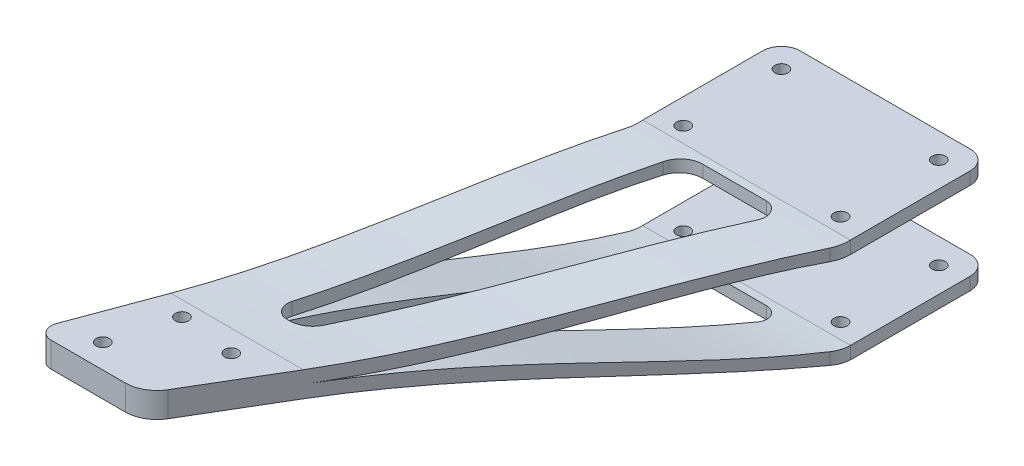
SolidWorks part; units mm, degrees
ref_plane "Front Plane" through (0, 0, 0) normal (0, 0, 1) x (1, 0, 0)
ref_plane "Top Plane" through (0, 0, 0) normal (0, 1, 0) x (1, 0, 0)
ref_plane "Right Plane" through (0, 0, 0) normal (1, 0, 0) x (0, 0, -1)
sketch "Sketch1" plane through (0, 0, 0) normal (0, 1, 0) x (1, 0, 0)
  line L0 (48.255, 28.1) -> (98.255, 28.1) construction
  line L1 (0, 0) -> (148.3533, 0) construction
  line L2 (0, 0) -> (0, 25) construction
  line L3 (0, 25) -> (148.3533, 25) construction
  line L4 (148.3533, 0) -> (148.3533, 25) construction
  line L5 (48.255, -3.1) -> (98.255, -3.1) construction
  line L6 (48.255, 26) -> (98.255, 26) construction
  line L7 (0, 12.5) -> (148.3533, 12.5) construction
  line L8 (-66.4765, -150) -> (240.8263, -150) construction
  line L9 (75.1995, 36.1) -> (100.255, 36.1)
  line L10 (106.255, 30.1) -> (106.255, -7.9752)
  line L11 (104.8547, -13.0786) -> (26.5055, -145.1034)
  line L12 (17.9058, -150) -> (-5.6524, -150)
  line L13 (-9.4032, -144.6102) -> (39.6319, -12.2766)
  line L14 (40.255, -8.8021) -> (40.255, 30.1)
  line L15 (46.255, 36.1) -> (75.1995, 36.1)
  circle A0 centre (48.255, 28.1) radius 2.1
  circle A1 centre (98.255, 28.1) radius 2.1
  circle A2 centre (98.255, -3.1) radius 2.1
  circle A3 centre (48.255, -3.1) radius 2.1
  arc A4 (100.255, 36.1) -> (106.255, 30.1) centre (100.255, 30.1) cw
  arc A5 (40.255, 30.1) -> (46.255, 36.1) centre (46.255, 30.1) cw
  arc A6 (26.5055, -145.1034) -> (17.9058, -150) centre (17.9058, -140) cw
  arc A7 (106.255, -7.9752) -> (104.8547, -13.0786) centre (96.255, -7.9752) cw
  arc A8 (39.6319, -12.2766) -> (40.255, -8.8021) centre (30.255, -8.8021) ccw
  arc A9 (-5.6524, -150) -> (-9.4032, -144.6102) centre (-5.6524, -146) cw
  point P32 (23.5997, -150)
  point P39 (-11.4003, -150)
  dimension "D2" = 4.2
  dimension "D7" = 8
  dimension "D10" = 6
  dimension "D11" = 10
  dimension "D12" = 4
  dimension "D1" = 25
  dimension "D3" = 1
  dimension "D4" = 50
  dimension "D5" = 150
  dimension "D6" = 35
  dimension "D8" = 8
  dimension "D9" = 8
extrude "Boss-Extrude1" add sketch "Sketch1" along normal blind 33
sketch "Sketch2" plane through (0, 33, 0) normal (0, 1, 0) x (1, 0, 0)
  line L0 (61.888, -10.4084) -> (81.9717, -10.4084)
  line L1 (85.4116, -16.4498) -> (33.9632, -103.1446)
  line L2 (27.0834, -107.0618) -> (26.2546, -107.0618)
  line L3 (22.5038, -101.672) -> (54.3865, -15.6288)
  line L4 (39.6319, -12.2766) -> (-9.4032, -144.6102) construction
  line L5 (26.5055, -145.1034) -> (104.8547, -13.0786) construction
  arc A0 (33.9632, -103.1446) -> (27.0834, -107.0618) centre (27.0834, -99.0618) cw
  arc A1 (61.888, -10.4084) -> (54.3865, -15.6288) centre (61.888, -18.4084) ccw
  arc A2 (26.2546, -107.0618) -> (22.5038, -101.672) centre (26.2546, -103.0618) cw
  arc A3 (81.9717, -10.4084) -> (85.4116, -16.4498) centre (81.9717, -14.4084) cw
  circle A4 centre (3.1113, -142.3521) radius 2.1
  circle A5 centre (26.5359, -124.9789) radius 2.1
  circle A6 centre (8.7723, -122.8765) radius 2.1
  dimension "D3" = 8
  dimension "D4" = 4
  dimension "D5" = 4.2
  dimension "D1" = 15
  dimension "D2" = 15
extrude "Cut-Extrude1" cut sketch "Sketch2" against normal through all
sketch "Sketch3" plane through (106.255, 0, 0) normal (1, 0, 0) x (0, 0, -1)
  line L0 (36.1, 16.5) -> (-150, 16.5) construction
  line L1 (36.1, 33) -> (36.1, 0) construction
  line L2 (-150, 33) -> (-150, 0) construction
  line L3 (-150, 16.5) -> (-7.9752, 29) construction
  line L5 (36.1, 29) -> (-7.9752, 29)
  line L6 (36.1, 29) -> (36.1, 4)
  line L7 (36.1, 4) -> (-7.9752, 4)
  line L8 (-118.0954, 20.5) -> (-150, 20.5)
  line L9 (-7.9752, 33) -> (30.1, 33) construction
  line L10 (-7.9752, 0) -> (30.1, 0) construction
  line L11 (-150, 20.5) -> (-150, 12.5)
  line L12 (-150, 12.5) -> (-118.0954, 12.5)
  line L13 (-7.9752, 0) -> (-150, 0)
  line L14 (-150, 0) -> (-150, 12.5)
  line L15 (-150, 20.5) -> (-150, 33)
  line L16 (-150, 33) -> (-7.9752, 33)
  line L17 (-145.1034, 33) -> (-13.0786, 33) construction
  line L18 (-7.9752, 33) -> (-7.9752, 0) construction
  spline S0 degree 3 poles (-7.9752, 29) (-41.31, 28.7998) (-72.9597, 16.3943) (-118.0954, 16.5) knots 0 0 0 0 1 1 1 1
  spline S1 degree 3 poles (-7.9752, 4) (-41.31, 4.2002) (-72.9597, 16.6057) (-118.0954, 16.5) knots 0 0 0 0 1 1 1 1
  spline S2 degree 3 poles (-118.0954, 20.5) (-78.3897, 20.5) (-43.5095, 31.0712) (-7.9752, 33) knots 0 0 0 0 1 1 1 1
  spline S3 degree 3 poles (-118.0954, 12.5) (-78.3897, 12.5) (-43.5095, 1.9288) (-7.9752, 0) knots 0 0 0 0 1 1 1 1
  point P8 (-7.9752, 29)
  point P29 (-150, 0)
  point P30 (-7.9752, 4)
  line M14 (30.1, 0) -> (30.1, 33)
  line M16 (-7.9752, 33) -> (-7.9752, 0)
  dimension "D1" = 4
  dimension "D2" = 4
extrude "Cut-Extrude2" cut sketch "Sketch3" against normal through all contours S3 L12 L14 L13 | L8 S2 L16 L15 | S1 S0 M16 | L7 L5 M14 M16 | L7 L6 L5 M14
